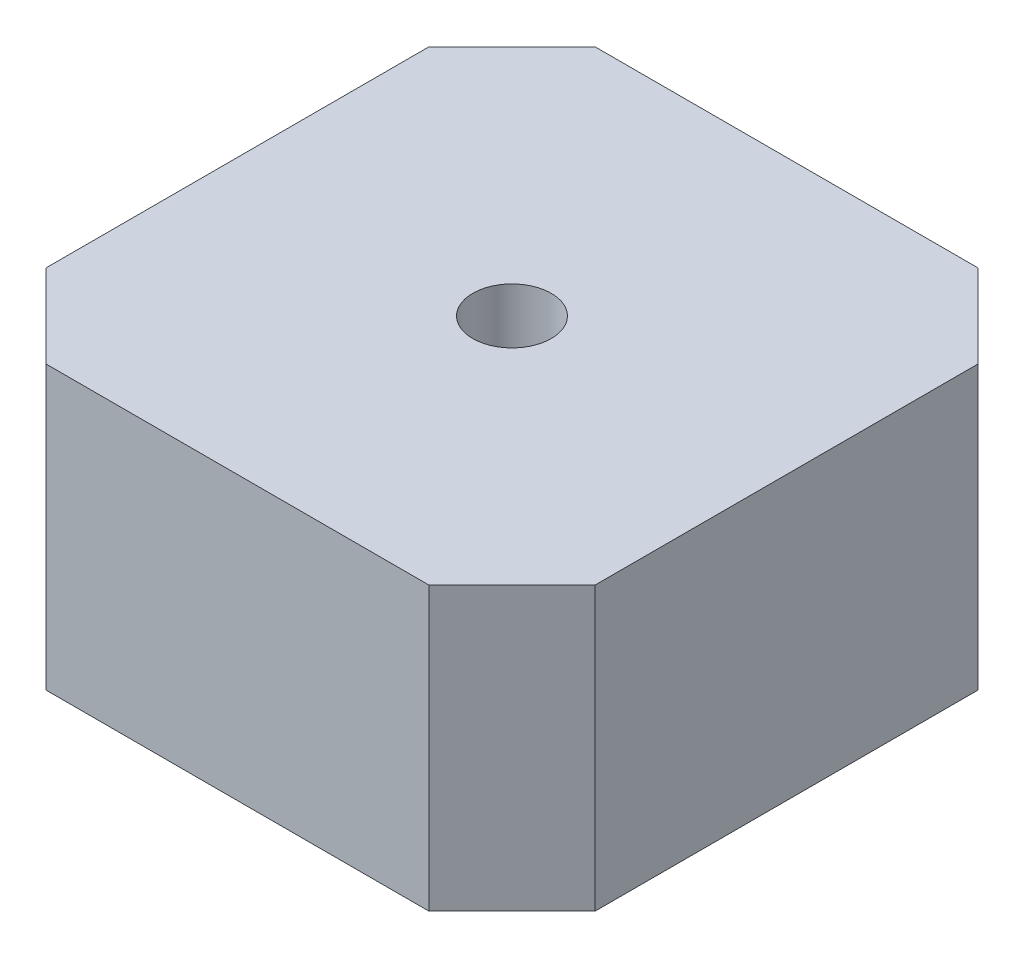
SolidWorks part; units mm, degrees
material "Hierro dúctil"
ref_plane "Alzado" through (0, 0, 0) normal (0, 0, 1) x (1, 0, 0)
ref_plane "Planta" through (0, 0, 0) normal (0, 1, 0) x (1, 0, 0)
ref_plane "Vista lateral" through (0, 0, 0) normal (1, 0, 0) x (0, 0, -1)
sketch "Croquis1" plane through (0, 0, 0) normal (0, 1, 0) x (1, 0, 0)
  line L1 (0, 0) -> (35, 0)
  line L2 (0, 0) -> (0, 35)
  line L3 (0, 35) -> (35, 35)
  line L4 (35, 0) -> (35, 35)
  dimension "D1" = 35
  dimension "D2" = 35
extrude "Saliente-Extruir1" add sketch "Croquis1" along normal blind 18
sketch "Croquis2" plane through (0, 18, 0) normal (0, 1, 0) x (1, 0, 0)
  line L0 (5.3015, 35) -> (0, 29.6985)
  line L1 (35, 35) -> (0, 35) construction
  line L2 (0, 35) -> (0, 0) construction
  line L3 (0, 29.6985) -> (0, 5.3015)
  line L4 (0, 5.3015) -> (5.3015, 0)
  line L5 (0, 0) -> (35, 0) construction
  line L6 (5.3015, 0) -> (29.6985, 0)
  line L7 (29.6985, 0) -> (35, 5.3015)
  line L8 (35, 0) -> (35, 35) construction
  line L9 (35, 5.3015) -> (35, 29.6985)
  line L10 (35, 29.6985) -> (29.6985, 35)
  line L11 (29.6985, 35) -> (5.3015, 35)
  dimension "D1" = 42
  dimension "D2" = 42
  dimension "D3" = 45
extrude "Cortar-Extruir2" cut sketch "Croquis2" against normal blind 18 flip side to cut
sketch "Croquis3" plane through (0, 18, 0) normal (0, 1, 0) x (1, 0, 0)
  line L0 (17.5, 35) -> (17.5, 0) construction
  line L1 (29.6985, 35) -> (5.3015, 35) construction
  line L2 (5.3015, 0) -> (29.6985, 0) construction
  circle A0 centre (17.5, 17.5) radius 2.5
  dimension "D1" = 5
extrude "Cortar-Extruir3" cut sketch "Croquis3" against normal through all
